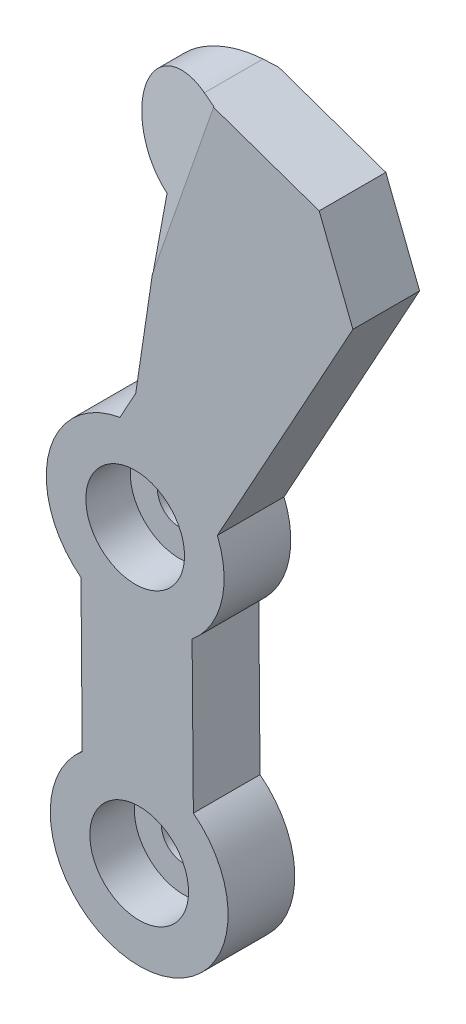
SolidWorks part; units mm, degrees
ref_plane "Front Plane" through (0, 0, 0) normal (0, 0, 1) x (1, 0, 0)
ref_plane "Top Plane" through (0, 0, 0) normal (0, 1, 0) x (1, 0, 0)
ref_plane "Right Plane" through (0, 0, 0) normal (1, 0, 0) x (0, 0, -1)
sketch "Sketch1" plane through (0, 0, 0) normal (0, 0, 1) x (1, 0, 0)
  line L0 (-0.8499, 17.4583) -> (0.0628, -47.5417) construction
  line L1 (5.5058, 85.326) -> (5.3078, 85.3936)
  line L2 (-13.0309, 1.6035) -> (-12.7512, -32.1859)
  line L3 (11.9643, 2.0941) -> (12.2436, -31.679)
  line L4 (17.6362, 25.116) -> (48.1292, 80.4952)
  line L5 (40.5387, 99.7888) -> (48.1292, 80.4952)
  line L6 (5.5058, 85.326) -> (-0.7156, 43.6177)
  line L8 (-0.8499, 17.4583) -> (38.1734, 87.2951) construction
  line L9 (-4.2703, 37.1618) -> (-0.7156, 43.6177)
  line L11 (38.1734, 87.2951) -> (9.8414, 97.1589) construction
  line L13 (40.5387, 99.7888) -> (13.9405, 109.0825)
  arc A0 (11.9643, 2.0941) -> (17.6362, 25.116) centre (-0.8397, 17.4583) ccw
  arc A4 (13.9405, 109.0825) -> (5.3078, 85.3936) centre (9.8414, 97.1589) ccw
  arc A6 (-4.2703, 37.1618) -> (-13.0309, 1.6035) centre (-0.8397, 17.4583) ccw
  arc A7 (-12.7512, -32.1859) -> (12.2436, -31.679) centre (0.0628, -47.5417) ccw
  point P2 (-0.3936, -25.0417)
  point P13 (18.4435, 32.4977)
  point P18 (23.5405, 72.3806)
  dimension "D5" = 30
  dimension "D6" = 80
  dimension "D7" = 65
  dimension "D11" = 40
  dimension "D12" = 40
  dimension "D1" = 0
  dimension "D2" = 210
  dimension "D3" = 0
  dimension "D4" = 80
  dimension "D13" = 0
  dimension "D14" = 0
extrude "Boss-Extrude1" add sketch "Sketch1" along normal blind 15
sketch "Sketch2" plane through (0, 0, 15) normal (0, 0, 1) x (1, 0, 0)
  circle A0 centre (-0.8397, 17.4583) radius 11.1
  circle A1 centre (0.0628, -47.5417) radius 11.1
  arc A2 (11.9643, 2.0941) -> (17.6362, 25.116) centre (-0.8397, 17.4583) ccw construction
  arc A3 (-12.7512, -32.1859) -> (12.2436, -31.679) centre (0.0628, -47.5417) ccw construction
  dimension "D4" = 22.2
  dimension "D5" = 22.2
  dimension "D1" = 0
  dimension "D2" = 0
  dimension "D3" = 0
extrude "Cut-Extrude1" cut sketch "Sketch2" against normal blind 10
sketch "Sketch3" plane through (0, 0, 5) normal (0, 0, 1) x (1, 0, 0)
  circle A0 centre (-0.8397, 17.4583) radius 5
  circle A1 centre (0.0628, -47.5417) radius 5
  circle A2 centre (-0.8397, 17.4583) radius 11.1 construction
  circle A3 centre (0.0628, -47.5417) radius 11.1 construction
  dimension "D3" = 10
  dimension "D4" = 10
  dimension "D1" = 0
  dimension "D2" = 0
extrude "Cut-Extrude2" cut sketch "Sketch3" against normal blind 10
sketch "Sketch6" plane through (35.4845, 101.5548, 0) normal (0.3299, 0.944, 0) x (0.944, -0.3299, 0)
  line L0 (-20.4188, -0.0852) -> (-37.6456, -6.977)
  line L1 (-37.6456, -6.977) -> (-37.6403, -10.8751)
  line L2 (-37.6403, -10.8751) -> (-19.7774, -14.8882)
extrude "Cut-Extrude-Thin3" cut sketch "Sketch6" against normal blind 63 thin
